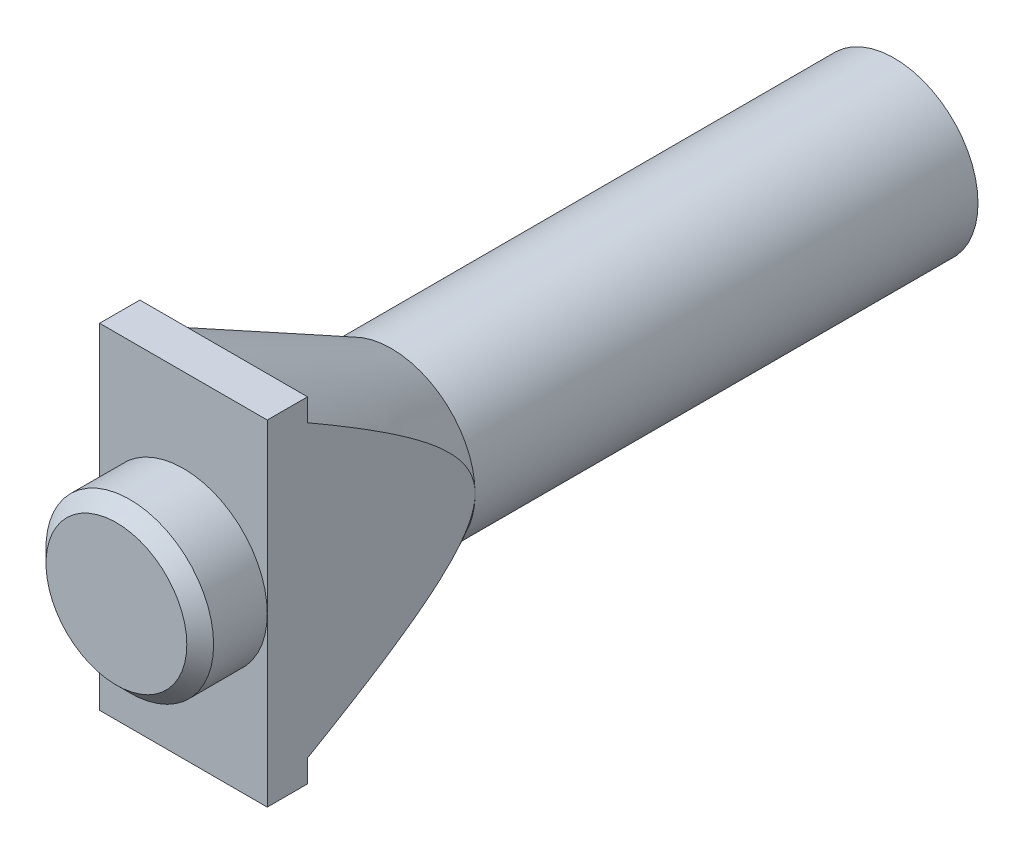
SolidWorks part; units mm, degrees
ref_plane "Front Plane" through (0, 0, 0) normal (0, 0, 1) x (1, 0, 0)
ref_plane "Top Plane" through (0, 0, 0) normal (0, 1, 0) x (1, 0, 0)
ref_plane "Right Plane" through (0, 0, 0) normal (1, 0, 0) x (0, 0, -1)
sketch "Sketch1" plane through (0, 0, 0) normal (0, 0, 1) x (1, 0, 0)
  circle A0 centre (0, 0) radius 6.25
  dimension "D1" = 12.5
extrude "Boss-Extrude1" add sketch "Sketch1" along normal blind 50
sketch "Sketch5" plane through (0, 0, 0) normal (1, 0, 0) x (0, 0, -1)
  line L0 (-63.5412, 0) -> (-78.0067, 0)
sketch "Sketch8" plane through (0, 0, 0) normal (0, 0, -1) x (-1, 0, 0)
  circle A0 centre (0, 0) radius 2.15
  dimension "D1" = 4.3
extrude "Cut-Extrude3" cut sketch "Sketch8" against normal blind 25
sketch "Sketch9" plane through (0, 0, 25) normal (0, 0, -1) x (-1, 0, 0)
  line L1 (4.1569, 0) -> (2.0785, 3.6)
  line L2 (2.0785, 3.6) -> (-2.0785, 3.6)
  line L3 (-2.0785, 3.6) -> (-4.1569, 0)
  line L4 (-4.1569, 0) -> (-2.0785, -3.6)
  line L5 (-2.0785, -3.6) -> (2.0785, -3.6)
  line L6 (2.0785, -3.6) -> (4.1569, 0)
  circle A0 centre (0, 0) radius 3.6 construction
  dimension "D1" = 7.2
extrude "Cut-Extrude4" cut sketch "Sketch9" against normal blind 3.5
sketch "Sketch10" plane through (0, 0, 50) normal (0, 0, 1) x (1, 0, 0)
  line L1 (6.25, 12.5) -> (-6.25, 12.5)
  line L2 (6.25, 12.5) -> (6.25, -12.5)
  line L3 (6.25, -12.5) -> (-6.25, -12.5)
  line L4 (-6.25, 12.5) -> (-6.25, -12.5)
  line L5 (6.25, 12.5) -> (-6.25, -12.5) construction
  line L6 (6.25, -12.5) -> (-6.25, 12.5) construction
  point P0 (0, 0)
  dimension "D1" = 25
  dimension "D2" = 12.5
extrude "Boss-Extrude2" add sketch "Sketch10" along normal blind 3
sketch "Sketch11" plane through (0, 0, 0) normal (1, 0, 0) x (0, 0, -1)
  line L0 (-50, 12.5) -> (-37.5, 6.25)
  line L1 (0, 6.25) -> (-50, 6.25) construction
  line L2 (-37.5, 6.25) -> (-37.5, 0)
  line L3 (-37.5, 0) -> (-50, 0)
  line L4 (-50, 0) -> (-50, 12.5)
  dimension "D1" = 12.5
revolve "Revolve1" add sketch "Sketch11" angle 360 about L0
sketch "Sketch12" plane through (0, 0, 53) normal (0, 0, 1) x (1, 0, 0)
  line L0 (-6.25, 12.5) -> (-6.25, -12.5)
  line L1 (-6.25, -12.5) -> (-13.5176, -12.5)
  line L2 (-13.5176, -12.5) -> (-13.5176, 12.5)
  line L3 (-13.5176, 12.5) -> (-6.25, 12.5)
  line L4 (6.25, 12.5) -> (6.25, -12.5)
  line L5 (6.25, -12.5) -> (15.6255, -12.5)
  line L6 (15.6255, -12.5) -> (15.6255, 12.5)
  line L7 (15.6255, 12.5) -> (6.25, 12.5)
extrude "Cut-Extrude5" cut sketch "Sketch12" against normal through all
sketch "Sketch13" plane through (0, 0, 28.5) normal (0, 0, -1) x (-1, 0, 0)
  circle A0 centre (0, 0) radius 2.15
extrude "Cut-Extrude6" cut sketch "Sketch13" against normal through all
sketch "Sketch14" plane through (0, 0, 53) normal (0, 0, 1) x (1, 0, 0)
  circle A0 centre (0, 0) radius 6.25
extrude "Boss-Extrude3" add sketch "Sketch14" along normal blind 5
chamfer "Chamfer1" distance 1 angle 45 1 edges at (6.25, 0, 58)
